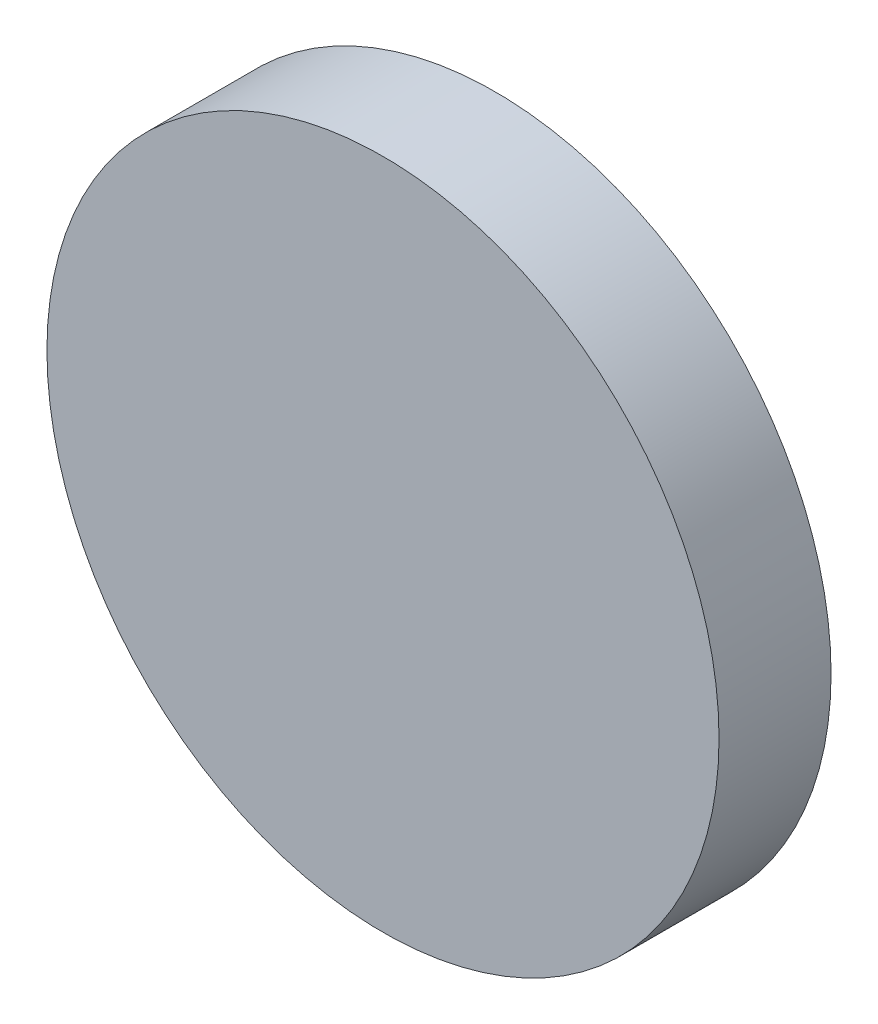
SolidWorks part; units mm, degrees
material "空气"
ref_plane "前视基准面" through (0, 0, 0) normal (0, 0, 1) x (1, 0, 0)
ref_plane "上视基准面" through (0, 0, 0) normal (0, 1, 0) x (1, 0, 0)
ref_plane "右视基准面" through (0, 0, 0) normal (1, 0, 0) x (0, 0, -1)
sketch "草图1" plane through (0, 0, 0) normal (0, 0, 1) x (1, 0, 0)
  circle A0 centre (0, 0) radius 6
  dimension "D1" = 12
extrude "凸台-拉伸1" add sketch "草图1" along normal blind 2
